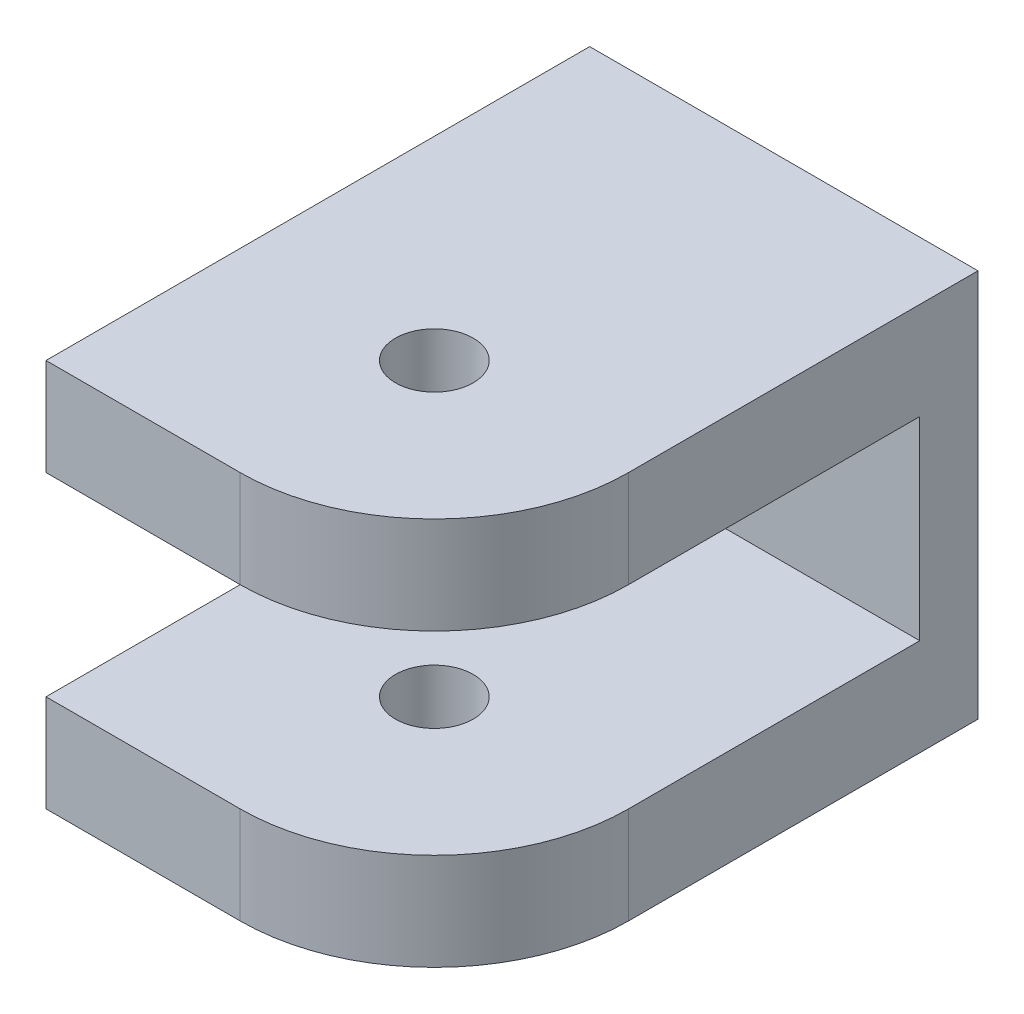
SolidWorks part; units mm, degrees
ref_plane "Alzado" through (0, 0, 0) normal (0, 0, 1) x (1, 0, 0)
ref_plane "Planta" through (0, 0, 0) normal (0, 1, 0) x (1, 0, 0)
ref_plane "Vista lateral" through (0, 0, 0) normal (1, 0, 0) x (0, 0, -1)
sketch "Croquis1" plane through (0, 0, 0) normal (0, 0, 1) x (1, 0, 0)
  line L0 (0, 0) -> (0, 20)
  line L1 (0, 20) -> (20, 20)
  line L2 (20, 20) -> (20, 0)
  line L3 (20, 0) -> (0, 0)
  circle A0 centre (10, 10) radius 1.55
  dimension "D5" = 3.1
  dimension "D1" = 20
  dimension "D2" = 20
  dimension "D3" = 10
  dimension "D4" = 10
extrude "Saliente-Extruir1" add sketch "Croquis1" against normal blind 3
sketch "Croquis2" plane through (0, 0, 0) normal (0, 0, 1) x (1, 0, 0)
  line L0 (0, 0) -> (20, 0)
  line L1 (20, 0) -> (20, 5)
  line L2 (20, 0) -> (20, 20) construction
  line L3 (20, 5) -> (0, 5)
  line L4 (0, 20) -> (0, 0) construction
  line L5 (0, 5) -> (0, 0)
  line L6 (0, 20) -> (20, 20)
  line L7 (20, 20) -> (20, 15)
  line L8 (20, 15) -> (0, 15)
  line L9 (0, 15) -> (0, 20)
  dimension "D1" = 5
  dimension "D2" = 5
extrude "Saliente-Extruir3" add sketch "Croquis2" along normal blind 15
sketch "Croquis3" plane through (0, 20, 0) normal (0, 1, 0) x (1, 0, 0)
  line L0 (20, -15) -> (0, -15) construction
  line L1 (20, -15) -> (0, -15)
  line L2 (0, -15) -> (0, -25)
  line L3 (10, -25) -> (0, -25)
  arc A0 (10, -25) -> (20, -15) centre (10, -15) ccw
extrude "Saliente-Extruir4" add sketch "Croquis3" against normal blind 5
sketch "Croquis4" plane through (0, 0, 0) normal (0, -1, 0) x (1, 0, 0)
  line L0 (0, 15) -> (20, 15) construction
  line L1 (0, 15) -> (20, 15)
  line L2 (0, 15) -> (0, 25)
  line L3 (0, 25) -> (10, 25)
  arc A0 (20, 15) -> (10, 25) centre (10, 15) ccw
extrude "Saliente-Extruir5" add sketch "Croquis4" against normal blind 5
sketch "Croquis5" plane through (0, 0, 0) normal (0, -1, 0) x (1, 0, 0)
  line L0 (0, -3) -> (0, 25) construction
  line L1 (10, 25) -> (0, 25) construction
  circle A0 centre (10, 15) radius 2
  dimension "D1" = 4
  dimension "D2" = 10
  dimension "D3" = 10
extrude "Cortar-Extruir1" cut sketch "Croquis5" against normal through all
